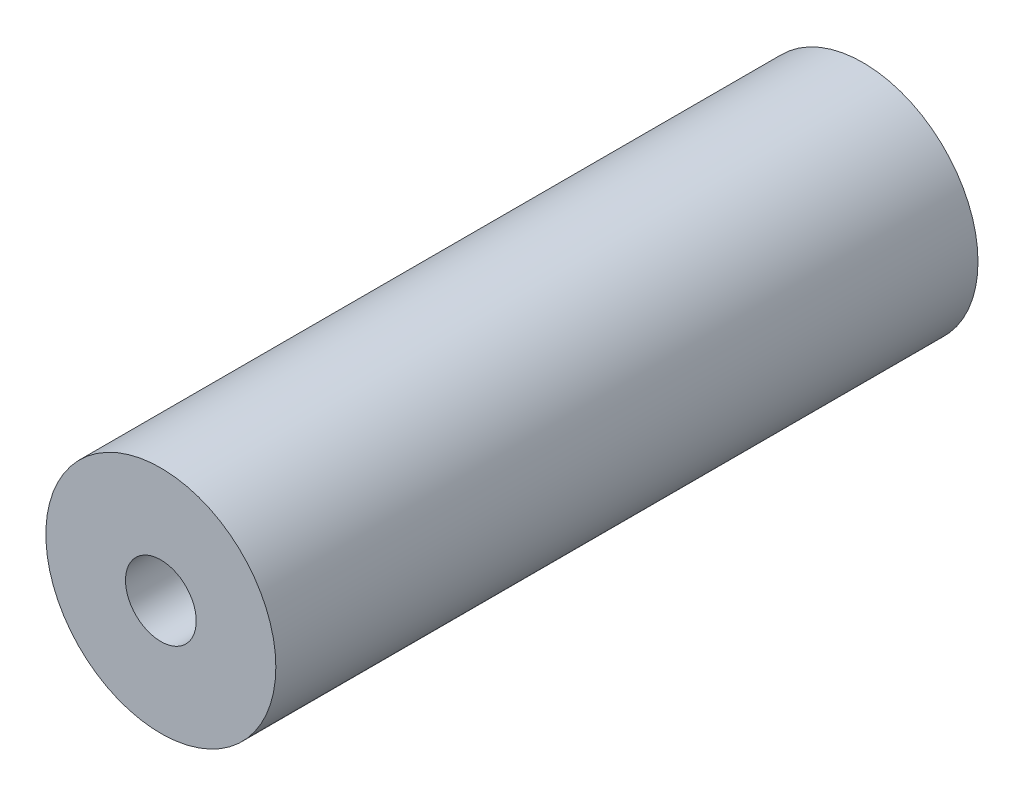
SolidWorks part; units mm, degrees
ref_plane "Front Plane" through (0, 0, 0) normal (0, 0, 1) x (1, 0, 0)
ref_plane "Top Plane" through (0, 0, 0) normal (0, 1, 0) x (1, 0, 0)
ref_plane "Right Plane" through (0, 0, 0) normal (1, 0, 0) x (0, 0, -1)
sketch "Sketch1" plane through (0, 0, 0) normal (0, 0, 1) x (1, 0, 0)
  circle A0 centre (0, 0) radius 6.5
  circle A1 centre (0, 0) radius 2
  dimension "D1" = 13
  dimension "D2" = 4
extrude "Boss-Extrude1" add sketch "Sketch1" against normal blind 39.6875
